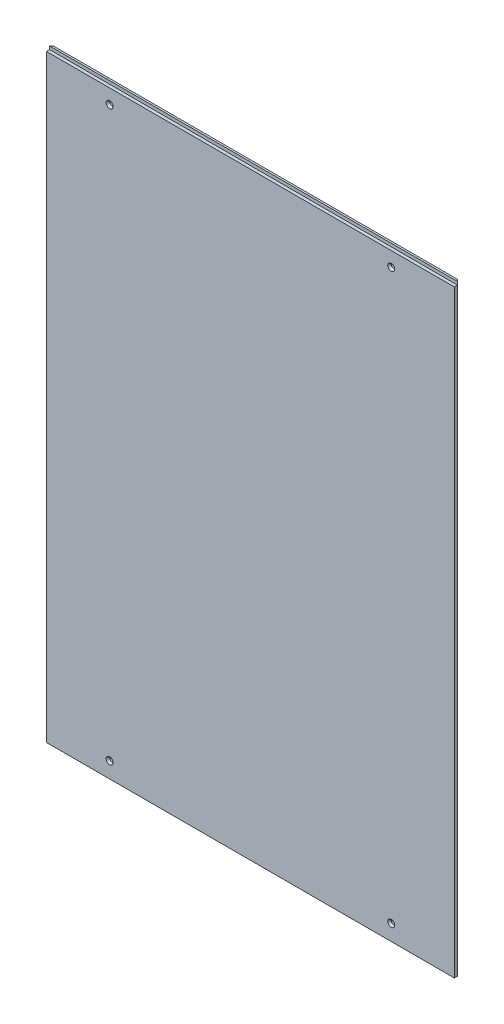
SolidWorks part; units mm, degrees
ref_plane "Front Plane" through (0, 0, 0) normal (0, 0, 1) x (1, 0, 0)
ref_plane "Top Plane" through (0, 0, 0) normal (0, 1, 0) x (1, 0, 0)
ref_plane "Right Plane" through (0, 0, 0) normal (1, 0, 0) x (0, 0, -1)
sketch "Sketch1" plane through (0, 0, 0) normal (0, 0, 1) x (1, 0, 0)
  line L1 (-323, -476.5) -> (323, -476.5)
  line L2 (-323, -476.5) -> (-323, 476.5)
  line L3 (-323, 476.5) -> (323, 476.5)
  line L4 (323, -476.5) -> (323, 476.5)
  line L5 (-323, -476.5) -> (323, 476.5) construction
  line L6 (-323, 476.5) -> (323, -476.5) construction
  point P0 (0, 0)
  dimension "Largura" = 646
  dimension "Altura" = 953
extrude "Boss-Extrude1" add sketch "Sketch1" along normal blind 8
chamfer "Chamfer1" distance 3 angle 45 2 edges at (-323, 0, 0) (323, 0, 0)
sketch "Sketch3" plane through (0, 0, 8) normal (0, 0, 1) x (1, 0, 0)
  line L0 (-323, 476.5) -> (-323, -476.5) construction
  line L1 (323, -476.5) -> (323, 476.5) construction
  line L2 (323, 476.5) -> (-323, 476.5) construction
  line L4 (-323, -476.5) -> (323, -476.5) construction
  circle A0 centre (-223, 448.5) radius 2.5
  circle A1 centre (-223, -451.5) radius 2.5
  circle A2 centre (223, -451.5) radius 2.5
  circle A3 centre (223, 448.5) radius 2.5
  dimension "D5" = 5
  dimension "D1" = 100
  dimension "D2" = 100
  dimension "D3" = 28
  dimension "D4" = 25
extrude "Cut-Extrude2" cut sketch "Sketch3" against normal through all
chamfer "Chamfer2" distance 3 angle 45 4 edges at (-220.5, -451.5, 8) (225.5, -451.5, 8) (225.5, 448.5, 8) (-220.5, 448.5, 8)
sketch "Sketch2" plane through (0, 0, 8) normal (0, 0, 1) x (1, 0, 0)
  line L0 (-323, 471.5) -> (323, 471.5)
  line L1 (323, 471.5) -> (323, 476.5)
  line L2 (323, 476.5) -> (-323, 476.5)
  line L3 (-323, 476.5) -> (-323, 471.5)
  line L4 (323, 476.5) -> (-323, 476.5) construction
  line L5 (-323, 476.5) -> (-323, -476.5) construction
  line L6 (323, -476.5) -> (323, 476.5) construction
  dimension "D1" = 5
extrude "Cut-Extrude3" cut sketch "Sketch2" against normal blind 5
